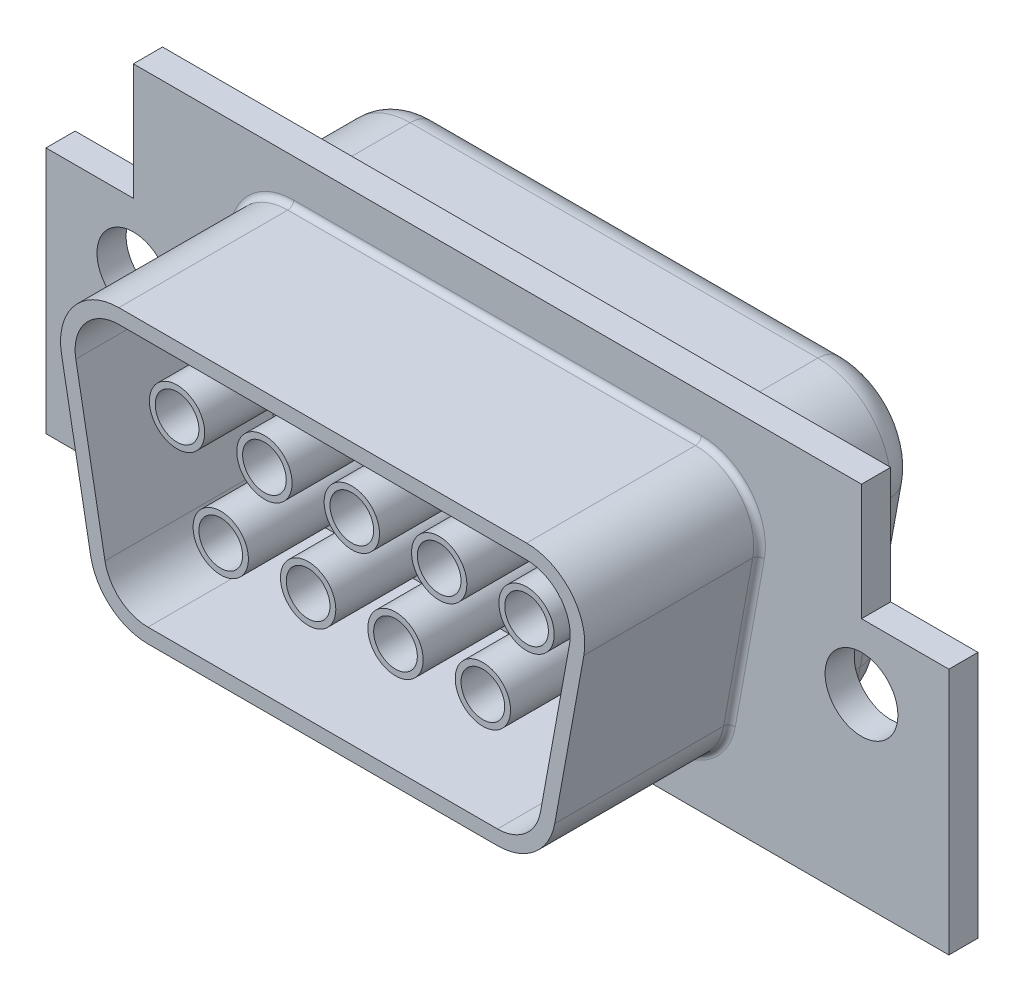
SolidWorks part; units mm, degrees
material "1060 Alloy"
ref_plane "Front Plane" through (0, 0, 0) normal (0, 0, 1) x (1, 0, 0)
ref_plane "Top Plane" through (0, 0, 0) normal (0, 1, 0) x (1, 0, 0)
ref_plane "Right Plane" through (0, 0, 0) normal (1, 0, 0) x (0, 0, -1)
sketch "Sketch1" plane through (0, 0, 0) normal (0, 0, 1) x (1, 0, 0)
  line L0 (-15.5, 6.25) -> (15.5, -6.25) construction
  line L1 (-15.5, 6.25) -> (15.5, 6.25)
  line L2 (-15.5, 6.25) -> (-15.5, -6.25)
  line L3 (-15.5, -6.25) -> (15.5, -6.25)
  line L4 (15.5, 6.25) -> (15.5, -6.25)
  point P4 (0, 0)
  dimension "D1" = 31
  dimension "D2" = 12.5
extrude "Extrude1" add sketch "Sketch1" along normal blind 1
sketch "Sketch2" plane through (0, 0, 1) normal (0, 0, 1) x (1, 0, 0)
  line L0 (-15.5, -6.25) -> (15.5, -6.25) construction
  line L1 (-7, 4.75) -> (7, 4.75)
  line L2 (-8.9677, 2.3922) -> (-7.9677, -3.1078)
  line L3 (-6, -4.75) -> (6, -4.75)
  line L4 (8.9677, 2.3922) -> (7.9677, -3.1078)
  line L5 (7.6692, -4.75) -> (13.0097, -4.8041) construction
  line L7 (-6, -4.25) -> (6, -4.25)
  line L8 (8.4758, 2.4817) -> (7.4758, -3.0183)
  line L9 (-7, 4.25) -> (7, 4.25)
  line L10 (-8.4758, 2.4817) -> (-7.4758, -3.0183)
  arc A0 (-7, 4.75) -> (-8.9677, 2.3922) centre (-7, 2.75) ccw
  arc A1 (8.9677, 2.3922) -> (7, 4.75) centre (7, 2.75) ccw
  arc A2 (-6, -4.75) -> (-7.9677, -3.1078) centre (-6, -2.75) cw
  arc A3 (7.9677, -3.1078) -> (6, -4.75) centre (6, -2.75) cw
  arc A4 (7.4758, -3.0183) -> (6, -4.25) centre (6, -2.75) cw
  arc A5 (8.4758, 2.4817) -> (7, 4.25) centre (7, 2.75) ccw
  arc A6 (-7, 4.25) -> (-8.4758, 2.4817) centre (-7, 2.75) ccw
  arc A7 (-6, -4.25) -> (-7.4758, -3.0183) centre (-6, -2.75) cw
  point P0 (0, 4.75)
  point P17 (0, -4.75)
  dimension "D3" = 2
  dimension "D4" = 2
  dimension "D2" = 2
  dimension "D1" = 14
  dimension "D5" = 9.5
  dimension "D6" = 1.5
  dimension "D7" = 12
extrude "Extrude2" add sketch "Sketch2" along normal blind 6
fillet "Fillet1" radius 0.2 8 edges at (8.5355, 4.0315, 1) (8.4677, -0.3578, 1) (7.2815, -4.2855, 1) (0, -4.75, 1) (-7.2815, -4.2855, 1) (-8.4677, -0.3578, 1) (-8.5355, 4.0315, 1) (0, 4.75, 1)
hole_wizard "M3x0.5 Tapped Hole1" positions "3DSketch1" profile "Sketch4" tap size "M3x0.5" standard "Ansi Metric"
sketch3d "3DSketch1"
  line L0 (-15.5, 6.25, 1) -> (-15.5, -6.25, 1) construction
  point P0 (-12.5, 0, 1)
  point P2 (12.5, 0, 1)
  point P7 (-15.5, 0, 1)
  dimension "D1" = 25
  dimension "D2" = 3
sketch "Sketch4" plane through (-12.5, 0, 1) normal (1, 0, 0) x (0, -1, 0)
  line L0 (0, 0) -> (0, 18.2511)
  line L1 (0, 18.2511) -> (1.25, 17.5)
  line L2 (1.25, 17.5) -> (1.25, 0)
  line L5 (1.25, 0) -> (0, 0)
  line L10 (0, 18.2511) -> (-1.25, 17.5) construction
  line L11 (0, -6.35) -> (0, 107.95) construction
  dimension "Tap Drill Dia." = 2.5
  dimension "Tap Drill Depth" = 17.5
  dimension "Drill Angle" = 118
cosmetic thread "Hole Thread1" parameters "D1"=1, "D2"=3
cosmetic thread "Hole Thread2" parameters "D1"=1, "D2"=3
sketch "Sketch6" plane through (0, 0, 0) normal (0, 0, -1) x (-1, 0, 0)
  line L8 (8.4597, -3.1972) -> (9.4597, 2.3028)
  line L9 (-6, -5.25) -> (6, -5.25)
  line L10 (-9.4597, 2.3028) -> (-8.4597, -3.1972)
  line L11 (7, 5.25) -> (-7, 5.25)
  line L12 (8.4597, -3.1972) -> (9.4597, 2.3028)
  line L13 (-6, -5.25) -> (6, -5.25)
  line L14 (-9.4597, 2.3028) -> (-8.4597, -3.1972)
  line L15 (7, 5.25) -> (-7, 5.25)
  arc A8 (9.4597, 2.3028) -> (7, 5.25) centre (7, 2.75) ccw
  arc A9 (6, -5.25) -> (8.4597, -3.1972) centre (6, -2.75) ccw
  arc A10 (-8.4597, -3.1972) -> (-6, -5.25) centre (-6, -2.75) ccw
  arc A11 (-7, 5.25) -> (-9.4597, 2.3028) centre (-7, 2.75) ccw
  arc A12 (9.4597, 2.3028) -> (7, 5.25) centre (7, 2.75) ccw
  arc A13 (6, -5.25) -> (8.4597, -3.1972) centre (6, -2.75) ccw
  arc A14 (-8.4597, -3.1972) -> (-6, -5.25) centre (-6, -2.75) ccw
  arc A15 (-7, 5.25) -> (-9.4597, 2.3028) centre (-7, 2.75) ccw
  dimension "D1" = 0.5
extrude "Extrude3" add sketch "Sketch6" along normal blind 4
fillet "Fillet2" radius 1 8 edges at (-8.9597, -0.4472, -4) (-7.6019, -4.6694, -4) (0, -5.25, -4) (7.6019, -4.6694, -4) (8.9597, -0.4472, -4) (8.9194, 4.3519, -4) (0, 5.25, -4) (-8.9194, 4.3519, -4)
sketch "Sketch7" plane through (0, 0, -4) normal (0, 0, -1) x (-1, 0, 0)
  line L8 (6.9839, -2.9289) -> (7.9839, 2.5711)
  line L9 (-6, -3.75) -> (6, -3.75)
  line L10 (-7.9839, 2.5711) -> (-6.9839, -2.9289)
  line L11 (7, 3.75) -> (-7, 3.75)
  line L12 (6.9839, -2.9289) -> (7.9839, 2.5711)
  line L13 (-6, -3.75) -> (6, -3.75)
  line L14 (-7.9839, 2.5711) -> (-6.9839, -2.9289)
  line L15 (7, 3.75) -> (-7, 3.75)
  arc A8 (7.9839, 2.5711) -> (7, 3.75) centre (7, 2.75) ccw
  arc A9 (6, -3.75) -> (6.9839, -2.9289) centre (6, -2.75) ccw
  arc A10 (-6.9839, -2.9289) -> (-6, -3.75) centre (-6, -2.75) ccw
  arc A11 (-7, 3.75) -> (-7.9839, 2.5711) centre (-7, 2.75) ccw
  arc A12 (7.9839, 2.5711) -> (7, 3.75) centre (7, 2.75) ccw
  arc A13 (6, -3.75) -> (6.9839, -2.9289) centre (6, -2.75) ccw
  arc A14 (-6.9839, -2.9289) -> (-6, -3.75) centre (-6, -2.75) ccw
  arc A15 (-7, 3.75) -> (-7.9839, 2.5711) centre (-7, 2.75) ccw
  dimension "D1" = 0.5
extrude "Extrude4" add sketch "Sketch7" along normal blind 0.5
sketch "Sketch8" plane through (0, 0, 1) normal (0, 0, 1) x (1, 0, 0)
  line L1 (1.5, -1.5) -> (-1.5, -1.5) construction
  circle A0 centre (-6, 1.5) radius 0.75
  circle A1 centre (-4.5, -1.5) radius 0.75
  circle A2 centre (-3, 1.5) radius 0.75
  circle A3 centre (1.5, -1.5) radius 0.75
  circle A4 centre (0, 1.5) radius 0.75
  circle A5 centre (-1.5, -1.5) radius 0.75
  circle A6 centre (3, 1.5) radius 0.75
  circle A7 centre (4.5, -1.5) radius 0.75
  circle A8 centre (6, 1.5) radius 0.75
  point P19 (0, -1.5)
  dimension "D1" = 1.5
  dimension "D4" = 1.5
  dimension "D5" = 1.5
  dimension "D6" = 1.5
  dimension "D7" = 1.5
  dimension "D8" = 1.5
  dimension "D9" = 1.5
  dimension "D10" = 1.5
  dimension "D11" = 1.5
  dimension "D2" = 3
  dimension "D3" = 1.5
  dimension "D12" = 3
  dimension "D13" = 3
  dimension "D14" = 3
  dimension "D15" = 1.5
  dimension "D16" = 3
  dimension "D17" = 3
  dimension "D18" = 3
extrude "Extrude-Thin2" add sketch "Sketch8" along normal blind 5 thin
sketch "Sketch10" plane through (0, 0, 1) normal (0, 0, 1) x (1, 0, 0)
  line L0 (15.5, 6.25) -> (-15.5, 6.25) construction
  line L1 (-18.9207, 8.4259) -> (-12.5, 8.4259)
  line L2 (-18.9207, 8.4259) -> (-18.9207, 2.25)
  line L3 (-18.9207, 2.25) -> (-12.5, 2.25)
  line L4 (-12.5, 8.4259) -> (-12.5, 2.25)
  line L5 (20.1371, 10.9942) -> (12.5, 10.9942)
  line L6 (20.1371, 10.9942) -> (20.1371, 2.25)
  line L7 (20.1371, 2.25) -> (12.5, 2.25)
  line L8 (12.5, 10.9942) -> (12.5, 2.25)
  line L9 (15.5, -6.25) -> (15.5, 6.25) construction
  line L10 (-15.5, 6.25) -> (-15.5, -6.25) construction
  dimension "D1" = 4
  dimension "D2" = 4
  dimension "D3" = 3
  dimension "D4" = 3
extrude "Cut-Extrude1" cut sketch "Sketch10" against normal blind 5
